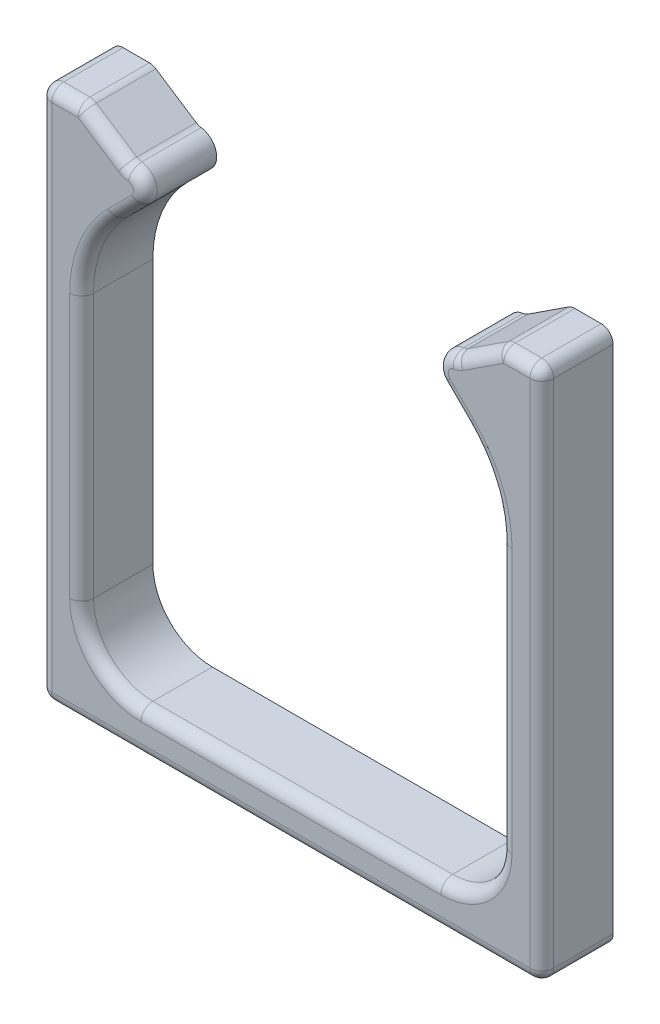
SolidWorks part; units mm, degrees
ref_plane "Front Plane" through (0, 0, 0) normal (0, 0, 1) x (1, 0, 0)
ref_plane "Top Plane" through (0, 0, 0) normal (0, 1, 0) x (1, 0, 0)
ref_plane "Right Plane" through (0, 0, 0) normal (1, 0, 0) x (0, 0, -1)
sketch "Sketch1" plane through (0, 0, 0) normal (0, 0, 1) x (1, 0, 0)
  line L0 (-156.7189, -40.9711) -> (-154.2093, -40.9711)
  line L2 (-121.9053, -3.0482) -> (-123.897, -1.0622)
  line L3 (-118.9664, -32.3844) -> (-118.9664, -10.1293)
  line L4 (-115.4568, 3.0289) -> (-115.4568, -39.9711)
  line L5 (-150.5532, 1.6407) -> (-153.9601, 3.8661)
  line L6 (-154.5069, 4.0289) -> (-156.7189, 4.0289)
  line L7 (-157.7189, 3.0289) -> (-157.7189, -39.9711)
  line L8 (-154.2093, -32.3844) -> (-154.2093, -10.1293)
  line L9 (-118.6687, 4.0289) -> (-116.4568, 4.0289)
  line L10 (-151.2703, -3.0482) -> (-149.2787, -1.0622)
  line L11 (-154.2093, -40.9711) -> (-116.8754, -40.9711)
  line L12 (-122.6224, 1.6407) -> (-119.2156, 3.8661)
  line L13 (-116.4568, -40.9711) -> (-118.9664, -40.9711)
  line L14 (-149.2093, -37.3844) -> (-123.9664, -37.3844)
  arc A0 (-149.2787, -1.0622) -> (-150.139, 1.4868) centre (-150.3378, 0) ccw
  arc A2 (-154.2093, -10.1293) -> (-151.2703, -3.0482) centre (-144.2093, -10.1293) cw
  arc A3 (-153.9601, 3.8661) -> (-154.5069, 4.0289) centre (-154.5069, 3.0289) ccw
  arc A4 (-157.7189, 3.0289) -> (-156.7189, 4.0289) centre (-156.7189, 3.0289) cw
  arc A5 (-150.139, 1.4868) -> (-150.5532, 1.6407) centre (-150.0064, 2.4779) cw
  arc A6 (-156.7189, -40.9711) -> (-157.7189, -39.9711) centre (-156.7189, -39.9711) cw
  arc A7 (-116.4568, -40.9711) -> (-115.4568, -39.9711) centre (-116.4568, -39.9711) ccw
  arc A8 (-123.0367, 1.4868) -> (-122.6224, 1.6407) centre (-123.1693, 2.4779) ccw
  arc A9 (-115.4568, 3.0289) -> (-116.4568, 4.0289) centre (-116.4568, 3.0289) ccw
  arc A10 (-119.2156, 3.8661) -> (-118.6687, 4.0289) centre (-118.6687, 3.0289) cw
  arc A11 (-118.9664, -10.1293) -> (-121.9053, -3.0482) centre (-128.9664, -10.1293) ccw
  arc A12 (-123.897, -1.0622) -> (-123.0367, 1.4868) centre (-122.8378, 0) cw
  arc A13 (-118.9664, -32.3844) -> (-123.9664, -37.3844) centre (-123.9664, -32.3844) cw
  arc A14 (-154.2093, -32.3844) -> (-149.2093, -37.3844) centre (-149.2093, -32.3844) ccw
  point P24 (-150.3378, 1.5)
  point P42 (-122.8378, 1.5)
  dimension "D1" = 10
  dimension "D2" = 1
  dimension "D3" = 1
  dimension "D4" = 5
extrude "Boss-Extrude1" add sketch "Sketch1" along normal blind 6 contours A14 L8 A2 L10 A0 A5 L5 A3 L6 A4 L7 A6 L0 L11 L13 A7 L4 A9 L9 A10 L12 A8 A12 L2 A11 L3 A13 L14
fillet "Fillet2" radius 1 26 edges at (-157.426, 3.736, 6) (-155.6129, 4.0289, 6) (-154.2217, 3.9873, 6) (-152.2567, 2.7534, 6) (-150.3547, 1.5406, 6) (-148.9166, 0.4797, 6) (-150.2745, -2.0552, 6) (-153.4454, -6.2959, 6) (-154.2093, -21.2568, 6) (-152.7448, -35.9199, 6) (-136.5878, -37.3844, 6) (-120.4308, -35.9199, 6) (-118.9664, -21.2568, 6) (-119.7303, -6.2959, 6) (-122.9012, -2.0552, 6) (-124.2591, 0.4797, 6) (-122.8209, 1.5406, 6) (-120.919, 2.7534, 6) (-118.954, 3.9873, 6) (-117.5627, 4.0289, 6) (-115.7497, 3.736, 6) (-115.4568, -18.4711, 6) (-115.7497, -40.6782, 6) (-136.5878, -40.9711, 6) (-157.426, -40.6782, 6) (-157.7189, -18.4711, 6)
